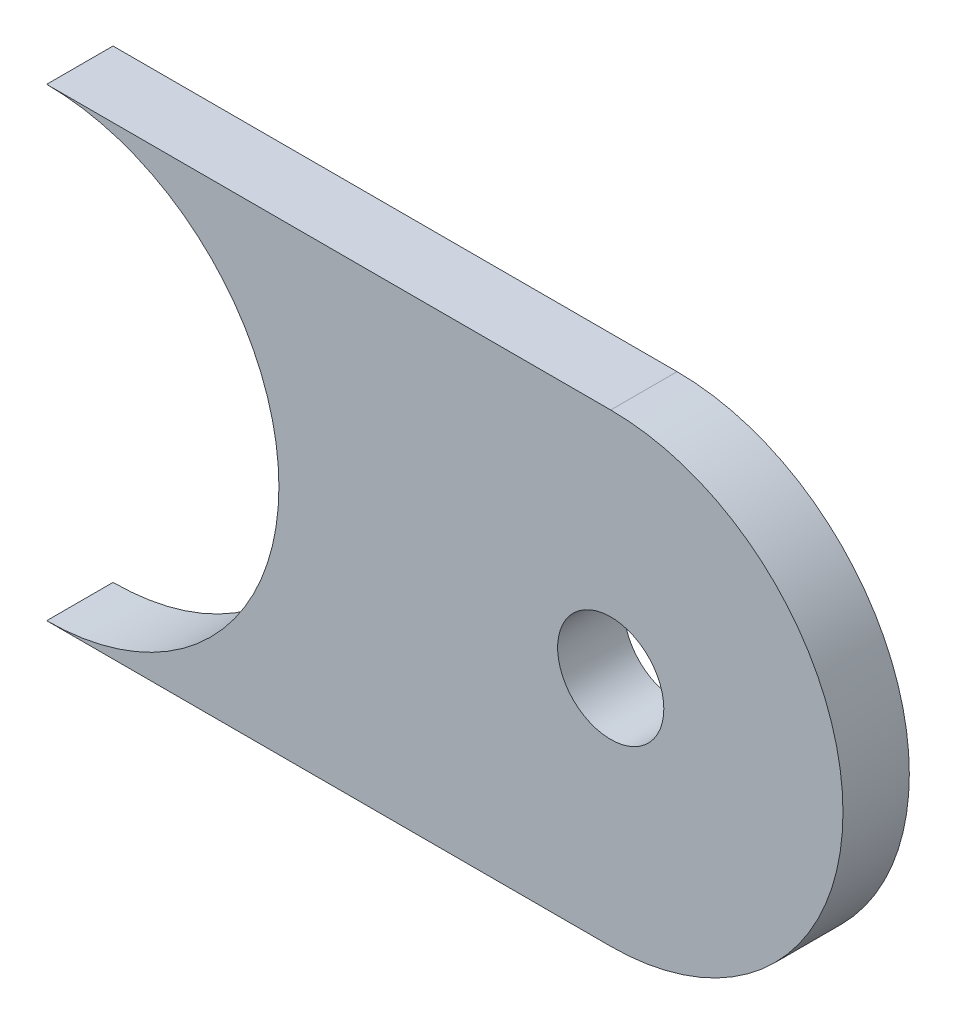
SolidWorks part; units mm, degrees
material "ASTM A36 Steel"
ref_plane "Front Plane" through (0, 0, 0) normal (0, 0, 1) x (1, 0, 0)
ref_plane "Top Plane" through (0, 0, 0) normal (0, 1, 0) x (1, 0, 0)
ref_plane "Right Plane" through (0, 0, 0) normal (1, 0, 0) x (0, 0, -1)
sketch "Sketch1" plane through (0, 0, 0) normal (0, 0, 1) x (1, 0, 0)
  line L1 (-39.8681, 25.0325) -> (2.6319, 25.0325)
  line L3 (-39.8681, -9.9675) -> (2.6319, -9.9675)
  arc A0 (2.6319, -9.9675) -> (2.6319, 25.0325) centre (2.6319, 7.5325) ccw
  arc A1 (-39.8681, 25.0325) -> (-39.8681, -9.9675) centre (-39.8681, 7.5325) cw
  circle A2 centre (2.6319, 7.5325) radius 4
extrude "Boss-Extrude1" add sketch "Sketch1" along normal blind 5
